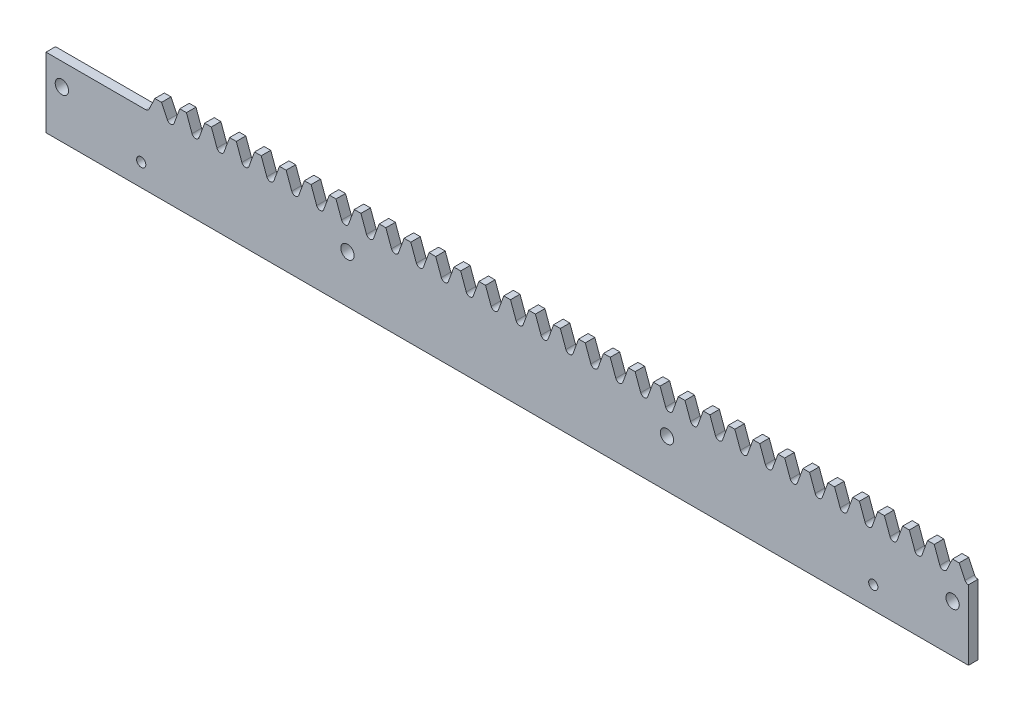
SolidWorks part; units mm, degrees
ref_plane "Plane1" through (0, 0, 0) normal (0, 0, 1) x (1, 0, 0)
ref_plane "Plane2" through (0, 0, 0) normal (0, 1, 0) x (1, 0, 0)
ref_plane "Plane3" through (0, 0, 0) normal (1, 0, 0) x (0, 0, -1)
sketch "Esquisse1" plane through (0, 0, 0) normal (0, 0, 1) x (1, 0, 0)
  line L0 (-11.781, 22) -> (19.635, 22)
  line L1 (23.5619, 29.1362) -> (23.5619, 19.2192) construction
  line L2 (-16.2297, 22) -> (24.6155, 22) construction
  line L3 (18.2522, 26.5) -> (283.3605, 26.5) construction
  line L4 (22.5084, 28.8854) -> (22.5084, 23.1798) construction
  line L5 (22.5084, 26.5) -> (20.6365, 22.5562)
  line L6 (24.6155, 26.5) -> (26.4874, 22.5562)
  line L8 (22.5084, 26.5) -> (24.6155, 26.5)
  line L10 (275.9429, 26.742) -> (275.9429, 19.9201) construction
  line L11 (273.8358, 26.742) -> (273.8358, 19.9201) construction
  line L12 (273.8358, 26.5) -> (272.0069, 22.6314)
  line L13 (275.9429, 26.5) -> (277.7718, 22.6314)
  line L14 (273.8358, 26.5) -> (275.9429, 26.5)
  line L20 (28.5976, 22.7763) -> (30.3624, 27.625)
  line L21 (30.3624, 27.625) -> (32.4695, 27.625)
  line L22 (34.2343, 22.7763) -> (32.4695, 27.625)
  line L23 (36.4515, 22.7763) -> (38.2163, 27.625)
  line L24 (38.2163, 27.625) -> (40.3235, 27.625)
  line L25 (42.0883, 22.7763) -> (40.3235, 27.625)
  line L26 (44.3055, 22.7763) -> (46.0703, 27.625)
  line L27 (46.0703, 27.625) -> (48.1775, 27.625)
  line L28 (49.9423, 22.7763) -> (48.1775, 27.625)
  line L29 (52.1595, 22.7763) -> (53.9243, 27.625)
  line L30 (53.9243, 27.625) -> (56.0314, 27.625)
  line L31 (57.7962, 22.7763) -> (56.0314, 27.625)
  line L32 (60.0135, 22.7763) -> (61.7783, 27.625)
  line L33 (61.7783, 27.625) -> (63.8854, 27.625)
  line L34 (65.6502, 22.7763) -> (63.8854, 27.625)
  line L35 (67.8675, 22.7763) -> (69.6323, 27.625)
  line L36 (69.6323, 27.625) -> (71.7394, 27.625)
  line L37 (73.5042, 22.7763) -> (71.7394, 27.625)
  line L38 (75.7215, 22.7763) -> (77.4862, 27.625)
  line L39 (77.4862, 27.625) -> (79.5934, 27.625)
  line L40 (81.3582, 22.7763) -> (79.5934, 27.625)
  line L41 (83.5754, 22.7763) -> (85.3402, 27.625)
  line L42 (85.3402, 27.625) -> (87.4474, 27.625)
  line L43 (89.2122, 22.7763) -> (87.4474, 27.625)
  line L44 (91.4294, 22.7763) -> (93.1942, 27.625)
  line L45 (93.1942, 27.625) -> (95.3013, 27.625)
  line L46 (97.0661, 22.7763) -> (95.3013, 27.625)
  line L47 (99.2834, 22.7763) -> (101.0482, 27.625)
  line L48 (101.0482, 27.625) -> (103.1553, 27.625)
  line L49 (104.9201, 22.7763) -> (103.1553, 27.625)
  line L50 (107.1374, 22.7763) -> (108.9022, 27.625)
  line L51 (108.9022, 27.625) -> (111.0093, 27.625)
  line L52 (112.7741, 22.7763) -> (111.0093, 27.625)
  line L53 (114.9914, 22.7763) -> (116.7562, 27.625)
  line L54 (116.7562, 27.625) -> (118.8633, 27.625)
  line L55 (120.6281, 22.7763) -> (118.8633, 27.625)
  line L56 (122.8453, 22.7763) -> (124.6101, 27.625)
  line L57 (124.6101, 27.625) -> (126.7173, 27.625)
  line L58 (128.4821, 22.7763) -> (126.7173, 27.625)
  line L59 (130.6993, 22.7763) -> (132.4641, 27.625)
  line L60 (132.4641, 27.625) -> (134.5713, 27.625)
  line L61 (136.3361, 22.7763) -> (134.5713, 27.625)
  line L62 (138.5533, 22.7763) -> (140.3181, 27.625)
  line L63 (140.3181, 27.625) -> (142.4252, 27.625)
  line L64 (144.19, 22.7763) -> (142.4252, 27.625)
  line L65 (146.4073, 22.7763) -> (148.1721, 27.625)
  line L66 (148.1721, 27.625) -> (150.2792, 27.625)
  line L67 (152.044, 22.7763) -> (150.2792, 27.625)
  line L68 (154.2613, 22.7763) -> (156.0261, 27.625)
  line L69 (156.0261, 27.625) -> (158.1332, 27.625)
  line L70 (159.898, 22.7763) -> (158.1332, 27.625)
  line L71 (162.1153, 22.7763) -> (163.88, 27.625)
  line L72 (163.88, 27.625) -> (165.9872, 27.625)
  line L73 (167.752, 22.7763) -> (165.9872, 27.625)
  line L74 (169.9692, 22.7763) -> (171.734, 27.625)
  line L75 (171.734, 27.625) -> (173.8412, 27.625)
  line L76 (175.606, 22.7763) -> (173.8412, 27.625)
  line L77 (177.8232, 22.7763) -> (179.588, 27.625)
  line L78 (179.588, 27.625) -> (181.6951, 27.625)
  line L79 (183.4599, 22.7763) -> (181.6951, 27.625)
  line L80 (185.6772, 22.7763) -> (187.442, 27.625)
  line L81 (187.442, 27.625) -> (189.5491, 27.625)
  line L82 (191.3139, 22.7763) -> (189.5491, 27.625)
  line L83 (193.5312, 22.7763) -> (195.296, 27.625)
  line L84 (195.296, 27.625) -> (197.4031, 27.625)
  line L85 (199.1679, 22.7763) -> (197.4031, 27.625)
  line L86 (201.3852, 22.7763) -> (203.15, 27.625)
  line L87 (203.15, 27.625) -> (205.2571, 27.625)
  line L88 (207.0219, 22.7763) -> (205.2571, 27.625)
  line L89 (209.2391, 22.7763) -> (211.0039, 27.625)
  line L90 (211.0039, 27.625) -> (213.1111, 27.625)
  line L91 (214.8759, 22.7763) -> (213.1111, 27.625)
  line L92 (217.0931, 22.7763) -> (218.8579, 27.625)
  line L93 (218.8579, 27.625) -> (220.9651, 27.625)
  line L94 (222.7298, 22.7763) -> (220.9651, 27.625)
  line L95 (224.9471, 22.7763) -> (226.7119, 27.625)
  line L96 (226.7119, 27.625) -> (228.819, 27.625)
  line L97 (230.5838, 22.7763) -> (228.819, 27.625)
  line L98 (232.8011, 22.7763) -> (234.5659, 27.625)
  line L99 (234.5659, 27.625) -> (236.673, 27.625)
  line L100 (238.4378, 22.7763) -> (236.673, 27.625)
  line L101 (240.6551, 22.7763) -> (242.4199, 27.625)
  line L102 (242.4199, 27.625) -> (244.527, 27.625)
  line L103 (246.2918, 22.7763) -> (244.527, 27.625)
  line L104 (248.509, 22.7763) -> (250.2738, 27.625)
  line L105 (250.2738, 27.625) -> (252.381, 27.625)
  line L106 (254.1458, 22.7763) -> (252.381, 27.625)
  line L107 (256.363, 22.7763) -> (258.1278, 27.625)
  line L108 (258.1278, 27.625) -> (260.235, 27.625)
  line L109 (261.9998, 22.7763) -> (260.235, 27.625)
  line L110 (264.217, 22.7763) -> (265.9818, 27.625)
  line L111 (265.9818, 27.625) -> (268.0889, 27.625)
  line L112 (269.8537, 22.7763) -> (268.0889, 27.625)
  line L114 (19.635, 37.0607) -> (19.635, -15.8181) construction
  line L115 (283.3605, 22) -> (228.0591, 22) construction
  line L118 (-11.781, 22) -> (-11.781, 0)
  line L121 (278.8759, 22.0015) -> (278.8759, 0)
  line L131 (278.8759, 0) -> (-11.781, 0)
  line L132 (133.5177, 28.2837) -> (133.5177, 9.5143) construction
  line L133 (130.5371, 22) -> (141.4123, 22) construction
  line L149 (273.8358, 27.625) -> (275.9429, 27.625) [skipped]
  line L150 (277.7077, 22.7763) -> (275.9429, 27.625) [skipped]
  line L151 (272.071, 22.7763) -> (273.8358, 27.625) [skipped]
  circle A0 centre (183.8759, 15) radius 2.1
  circle A1 centre (83.219, 15) radius 2.1
  arc A7 (19.635, 22) -> (20.6365, 22.5562) centre (19.635, 23.1798) ccw
  arc A8 (27.4889, 22) -> (26.4874, 22.5562) centre (27.4889, 23.1798) cw
  arc A9 (27.4889, 22) -> (28.5976, 22.7763) centre (27.4889, 23.1798) ccw
  arc A10 (35.3429, 22) -> (34.2343, 22.7763) centre (35.3429, 23.1798) cw
  arc A11 (35.3429, 22) -> (36.4515, 22.7763) centre (35.3429, 23.1798) ccw
  arc A12 (43.1969, 22) -> (42.0883, 22.7763) centre (43.1969, 23.1798) cw
  arc A13 (43.1969, 22) -> (44.3055, 22.7763) centre (43.1969, 23.1798) ccw
  arc A14 (51.0509, 22) -> (49.9423, 22.7763) centre (51.0509, 23.1798) cw
  arc A15 (51.0509, 22) -> (52.1595, 22.7763) centre (51.0509, 23.1798) ccw
  arc A16 (58.9049, 22) -> (57.7962, 22.7763) centre (58.9049, 23.1798) cw
  arc A17 (58.9049, 22) -> (60.0135, 22.7763) centre (58.9049, 23.1798) ccw
  arc A18 (66.7588, 22) -> (65.6502, 22.7763) centre (66.7588, 23.1798) cw
  arc A19 (66.7588, 22) -> (67.8675, 22.7763) centre (66.7588, 23.1798) ccw
  arc A20 (74.6128, 22) -> (73.5042, 22.7763) centre (74.6128, 23.1798) cw
  arc A21 (74.6128, 22) -> (75.7215, 22.7763) centre (74.6128, 23.1798) ccw
  arc A22 (82.4668, 22) -> (81.3582, 22.7763) centre (82.4668, 23.1798) cw
  arc A23 (82.4668, 22) -> (83.5754, 22.7763) centre (82.4668, 23.1798) ccw
  arc A24 (90.3208, 22) -> (89.2122, 22.7763) centre (90.3208, 23.1798) cw
  arc A25 (90.3208, 22) -> (91.4294, 22.7763) centre (90.3208, 23.1798) ccw
  arc A26 (98.1748, 22) -> (97.0661, 22.7763) centre (98.1748, 23.1798) cw
  arc A27 (98.1748, 22) -> (99.2834, 22.7763) centre (98.1748, 23.1798) ccw
  arc A28 (106.0288, 22) -> (104.9201, 22.7763) centre (106.0288, 23.1798) cw
  arc A29 (106.0288, 22) -> (107.1374, 22.7763) centre (106.0288, 23.1798) ccw
  arc A30 (113.8827, 22) -> (112.7741, 22.7763) centre (113.8827, 23.1798) cw
  arc A31 (113.8827, 22) -> (114.9914, 22.7763) centre (113.8827, 23.1798) ccw
  arc A32 (121.7367, 22) -> (120.6281, 22.7763) centre (121.7367, 23.1798) cw
  arc A33 (121.7367, 22) -> (122.8453, 22.7763) centre (121.7367, 23.1798) ccw
  arc A34 (129.5907, 22) -> (128.4821, 22.7763) centre (129.5907, 23.1798) cw
  arc A35 (129.5907, 22) -> (130.6993, 22.7763) centre (129.5907, 23.1798) ccw
  arc A36 (137.4447, 22) -> (136.3361, 22.7763) centre (137.4447, 23.1798) cw
  arc A37 (137.4447, 22) -> (138.5533, 22.7763) centre (137.4447, 23.1798) ccw
  arc A38 (145.2987, 22) -> (144.19, 22.7763) centre (145.2987, 23.1798) cw
  arc A39 (145.2987, 22) -> (146.4073, 22.7763) centre (145.2987, 23.1798) ccw
  arc A40 (153.1526, 22) -> (152.044, 22.7763) centre (153.1526, 23.1798) cw
  arc A41 (153.1526, 22) -> (154.2613, 22.7763) centre (153.1526, 23.1798) ccw
  arc A42 (161.0066, 22) -> (159.898, 22.7763) centre (161.0066, 23.1798) cw
  arc A43 (161.0066, 22) -> (162.1153, 22.7763) centre (161.0066, 23.1798) ccw
  arc A44 (168.8606, 22) -> (167.752, 22.7763) centre (168.8606, 23.1798) cw
  arc A45 (168.8606, 22) -> (169.9692, 22.7763) centre (168.8606, 23.1798) ccw
  arc A46 (176.7146, 22) -> (175.606, 22.7763) centre (176.7146, 23.1798) cw
  arc A47 (176.7146, 22) -> (177.8232, 22.7763) centre (176.7146, 23.1798) ccw
  arc A48 (184.5686, 22) -> (183.4599, 22.7763) centre (184.5686, 23.1798) cw
  arc A49 (184.5686, 22) -> (185.6772, 22.7763) centre (184.5686, 23.1798) ccw
  arc A50 (192.4226, 22) -> (191.3139, 22.7763) centre (192.4226, 23.1798) cw
  arc A51 (192.4226, 22) -> (193.5312, 22.7763) centre (192.4226, 23.1798) ccw
  arc A52 (200.2765, 22) -> (199.1679, 22.7763) centre (200.2765, 23.1798) cw
  arc A53 (200.2765, 22) -> (201.3852, 22.7763) centre (200.2765, 23.1798) ccw
  arc A54 (208.1305, 22) -> (207.0219, 22.7763) centre (208.1305, 23.1798) cw
  arc A55 (208.1305, 22) -> (209.2391, 22.7763) centre (208.1305, 23.1798) ccw
  arc A56 (215.9845, 22) -> (214.8759, 22.7763) centre (215.9845, 23.1798) cw
  arc A57 (215.9845, 22) -> (217.0931, 22.7763) centre (215.9845, 23.1798) ccw
  arc A58 (223.8385, 22) -> (222.7298, 22.7763) centre (223.8385, 23.1798) cw
  arc A59 (223.8385, 22) -> (224.9471, 22.7763) centre (223.8385, 23.1798) ccw
  arc A60 (231.6925, 22) -> (230.5838, 22.7763) centre (231.6925, 23.1798) cw
  arc A61 (231.6925, 22) -> (232.8011, 22.7763) centre (231.6925, 23.1798) ccw
  arc A62 (239.5464, 22) -> (238.4378, 22.7763) centre (239.5464, 23.1798) cw
  arc A63 (239.5464, 22) -> (240.6551, 22.7763) centre (239.5464, 23.1798) ccw
  arc A64 (247.4004, 22) -> (246.2918, 22.7763) centre (247.4004, 23.1798) cw
  arc A65 (247.4004, 22) -> (248.509, 22.7763) centre (247.4004, 23.1798) ccw
  arc A66 (255.2544, 22) -> (254.1458, 22.7763) centre (255.2544, 23.1798) cw
  arc A67 (255.2544, 22) -> (256.363, 22.7763) centre (255.2544, 23.1798) ccw
  arc A68 (263.1084, 22) -> (261.9998, 22.7763) centre (263.1084, 23.1798) cw
  arc A69 (263.1084, 22) -> (264.217, 22.7763) centre (263.1084, 23.1798) ccw
  arc A70 (270.9624, 22) -> (269.8537, 22.7763) centre (270.9624, 23.1798) cw
  arc A72 (270.9624, 22) -> (272.0069, 22.6314) centre (270.9624, 23.1798) ccw
  arc A79 (278.8759, 22.0015) -> (277.7718, 22.6314) centre (278.8163, 23.1798) cw
  circle A81 centre (-6.781, 15) radius 2.1
  circle A82 centre (273.8759, 15) radius 2.1
  dimension "D2" = 4.5
  dimension "D3" = 4.2
  dimension "D8" = 290.6568
  dimension "D9" = 90
  dimension "D10" = 5
  dimension "D11" = 90
  dimension "D7" = 5
  dimension "D12" = 100.6568
  dimension "D13" = 15
  dimension "D14" = 11.781
extrude "Extrusion1" add sketch "Esquisse1" along normal blind 3
sketch "Esquisse4" plane through (0, 0, 3) normal (0, 0, 1) x (1, 0, 0)
  line L0 (278.8759, 0) -> (-11.781, 0) construction
  line L1 (278.8759, 22.0015) -> (278.8759, 0) construction
  line L2 (-11.781, 22) -> (-11.781, 0) construction
  circle A0 centre (18.219, 7) radius 1.45
  circle A2 centre (248.8759, 7) radius 1.45
  dimension "D1" = 2.9
  dimension "D2" = 7
  dimension "D3" = 30
  dimension "D4" = 30
extrude "Enlèv. mat.-Extru.2" cut sketch "Esquisse4" against normal through all
